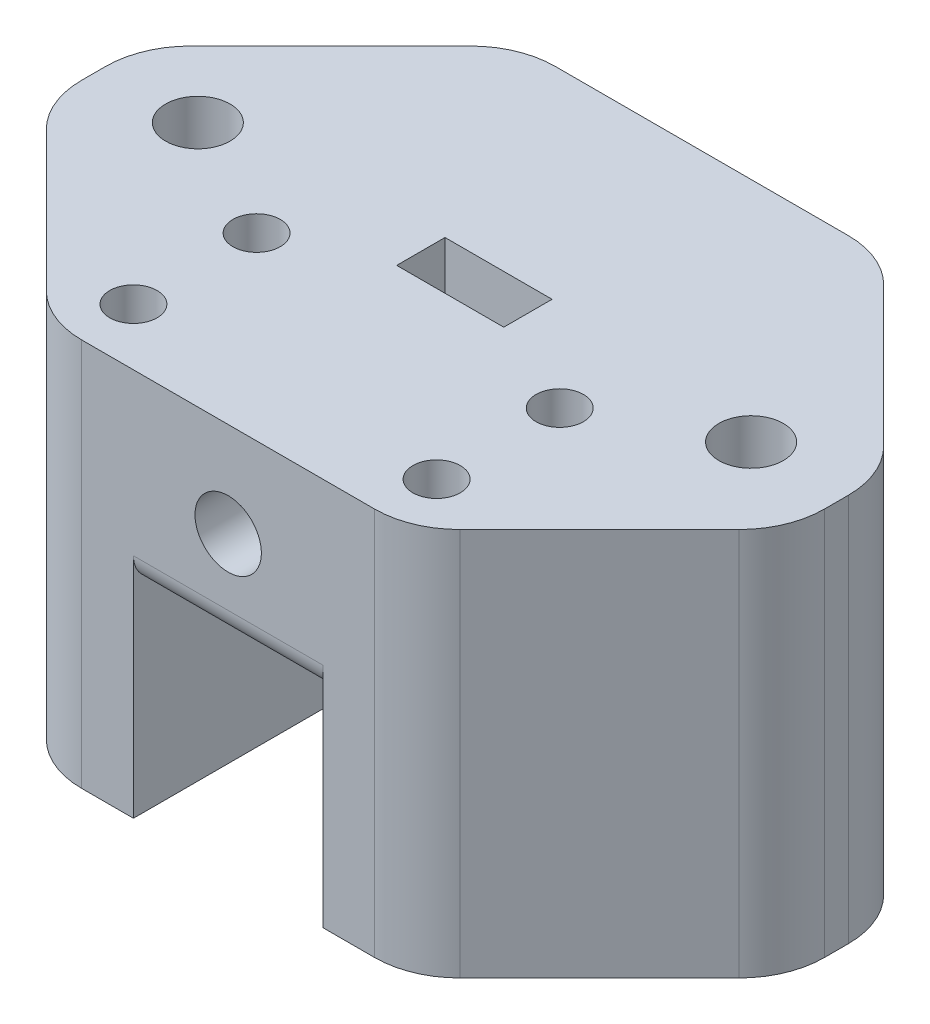
SolidWorks part; units mm, degrees
material "ABS PC"
ref_plane "Front Plane" through (0, 0, 0) normal (0, 0, 1) x (1, 0, 0)
ref_plane "Top Plane" through (0, 0, 0) normal (0, 1, 0) x (1, 0, 0)
ref_plane "Right Plane" through (0, 0, 0) normal (1, 0, 0) x (0, 0, -1)
sketch "Sketch1" plane through (0, 0, 0) normal (0, 1, 0) x (1, 0, 0)
  line L0 (0, 0) -> (0, 25)
  line L1 (0, 0) -> (39.2, 0)
  line L2 (0, 25) -> (39.2, 25)
  line L3 (39.2, 0) -> (39.2, 25)
  dimension "D1" = 39.2
  dimension "D2" = 25
extrude "Boss-Extrude1" add sketch "Sketch1" along normal blind 10
hole_wizard "Ø3.5 (3.5) Diameter Hole1" positions "Sketch8" profile "Sketch7" hole size "Ø3.5" standard "ANSI Metric" end condition through all
sketch "Sketch8" plane through (0, 0, -25) normal (0, 0, -1) x (-1, 0, 0)
  line L2 (0, 10) -> (0, 0) construction
  line L3 (-39.2, 0) -> (0, 0) construction
  point P0 (-19.6, 5)
  point P15 (-19.6, 0)
  dimension "D1" = 19.6
  dimension "D2" = 5
sketch "Sketch7" plane through (19.6, 5, -25) normal (1, 0, 0) x (0, 1, 0)
  line L0 (0, 0) -> (0, 25)
  line L1 (0, 25) -> (1.75, 25)
  line L2 (1.75, 25) -> (1.75, 0)
  line L5 (1.75, 0) -> (0, 0)
  line L11 (0, -6.35) -> (0, 107.95) construction
  dimension "Thru Hole Dia." = 3.5
  dimension "Thru Hole Depth" = 25
sketch "Sketch9" plane through (0, 0, 0) normal (0, -1, 0) x (1, 0, 0)
  line L0 (39.2, -25) -> (39.2, 0)
  line L1 (39.2, -25) -> (24.6, -25)
  line L2 (39.2, 0) -> (24.6, 0)
  line L3 (24.6, -25) -> (24.6, 0)
  line L4 (0, -25) -> (0, 0)
  line L5 (0, -25) -> (14.6, -25)
  line L6 (0, 0) -> (14.6, 0)
  line L7 (14.6, -25) -> (14.6, 0)
  dimension "D1" = 10
  dimension "D2" = 14.6
extrude "Boss-Extrude2" add sketch "Sketch9" along normal blind 10.5
sketch "Sketch10" plane through (0, 10, 0) normal (0, 1, 0) x (1, 0, 0)
  line L0 (16.775, 11.72) -> (22.425, 11.72)
  line L1 (16.775, 11.72) -> (16.775, 14.27)
  line L2 (22.425, 11.72) -> (22.425, 14.27)
  line L3 (16.775, 14.27) -> (22.425, 14.27)
  line L4 (0, 25) -> (0, 0) construction
  line L5 (39.2, 25) -> (0, 25) construction
  dimension "D1" = 5.65
  dimension "D2" = 2.55
  dimension "D3" = 16.775
  dimension "D4" = 10.73
extrude "Cut-Extrude4" cut sketch "Sketch10" against normal blind 10
hole_wizard "Ø2.5 (2.5) Diameter Hole1" positions "Sketch12" profile "Sketch11" hole size "Ø2.5" standard "ANSI Metric"
sketch "Sketch12" plane through (0, 10, 0) normal (0, 1, 0) x (1, 0, 0)
  line L0 (0, 0) -> (39.2, 0) construction
  line L1 (39.2, 0) -> (39.2, 25) construction
  point P0 (11.6, 3)
  point P2 (27.6, 3)
  point P4 (27.6, 9.5)
  point P6 (11.6, 9.5)
  dimension "D1" = 3
  dimension "D2" = 6.5
  dimension "D3" = 16
  dimension "D4" = 11.6
sketch "Sketch11" plane through (11.6, 10, -3) normal (1, 0, 0) x (0, 0, 1)
  line L0 (0, 0) -> (0, 7.7511)
  line L1 (0, 7.7511) -> (1.25, 7)
  line L2 (1.25, 7) -> (1.25, 0)
  line L5 (1.25, 0) -> (0, 0)
  line L10 (0, 7.7511) -> (-1.25, 7) construction
  line L11 (0, -6.35) -> (0, 107.95) construction
  dimension "Hole Dia." = 2.5
  dimension "Hole Depth" = 7
  dimension "Drill Angle" = 118
hole_wizard "Ø3.4 (3.4) Diameter Hole1" positions "Sketch3" profile "Sketch2" hole size "Ø3.4" standard "ANSI Metric" end condition through all
sketch "Sketch3" plane through (0, 10, 0) normal (0, 1, 0) x (1, 0, 0)
  line L0 (0, 25) -> (0, 0) construction
  line L1 (39.2, 0) -> (39.2, 25) construction
  line L3 (39.2, 25) -> (0, 25) construction
  point P0 (34.2, 13)
  point P2 (5, 13)
  dimension "D1" = 5
  dimension "D2" = 5
  dimension "D4" = 12
sketch "Sketch2" plane through (34.2, 10, -13) normal (1, 0, 0) x (0, 0, 1)
  line L0 (0, 0) -> (0, 20.5)
  line L1 (0, 20.5) -> (1.7, 20.5)
  line L2 (1.7, 20.5) -> (1.7, 0)
  line L5 (1.7, 0) -> (0, 0)
  line L11 (0, -6.35) -> (0, 107.95) construction
  dimension "Thru Hole Dia." = 3.4
  dimension "Thru Hole Depth" = 20.5
chamfer "Chamfer1" distance 10 angle 45 4 edges at (0, -0.25, -25) (0, -0.25, 0) (39.2, -0.25, 0) (39.2, -0.25, -25)
fillet "Fillet5" radius 4.5 8 edges at (29.2, -0.25, 0) (10, -0.25, 0) (0, -0.25, -10) (0, -0.25, -15) (10, -0.25, -25) (29.2, -0.25, -25) (39.2, -0.25, -10) (39.2, -0.25, -15)
fillet "Fillet6" radius 1.5 1 edges
hole_wizard "Ø3.4 (3.4) Diameter Hole2" positions "Sketch14" profile "Sketch13" hole size "Ø3.4" standard "ANSI Metric"
sketch "Sketch14" plane through (0, -10.5, 0) normal (0, -1, 0) x (-1, 0, 0)
  line L1 (-24.6, 25) -> (-27.336, 25) construction
  circle A1 centre (-34.2, 13) radius 1.7 construction
  circle A2 centre (-5, 13) radius 1.7 construction
  point P0 (-9.6, 13)
  point P2 (-29.6, 13)
  dimension "D3" = 4.6
  dimension "D1" = 12
  dimension "D2" = 4.6
sketch "Sketch13" plane through (9.6, -10.5, -13) normal (1, 0, 0) x (0, 0, -1)
  line L0 (0, 0) -> (0, 5.0215)
  line L1 (0, 5.0215) -> (1.7, 4)
  line L2 (1.7, 4) -> (1.7, 0)
  line L5 (1.7, 0) -> (0, 0)
  line L10 (0, 5.0215) -> (-1.7, 4) construction
  line L11 (0, -6.35) -> (0, 107.95) construction
  dimension "Hole Dia." = 3.4
  dimension "Hole Depth" = 4
  dimension "Drill Angle" = 118
